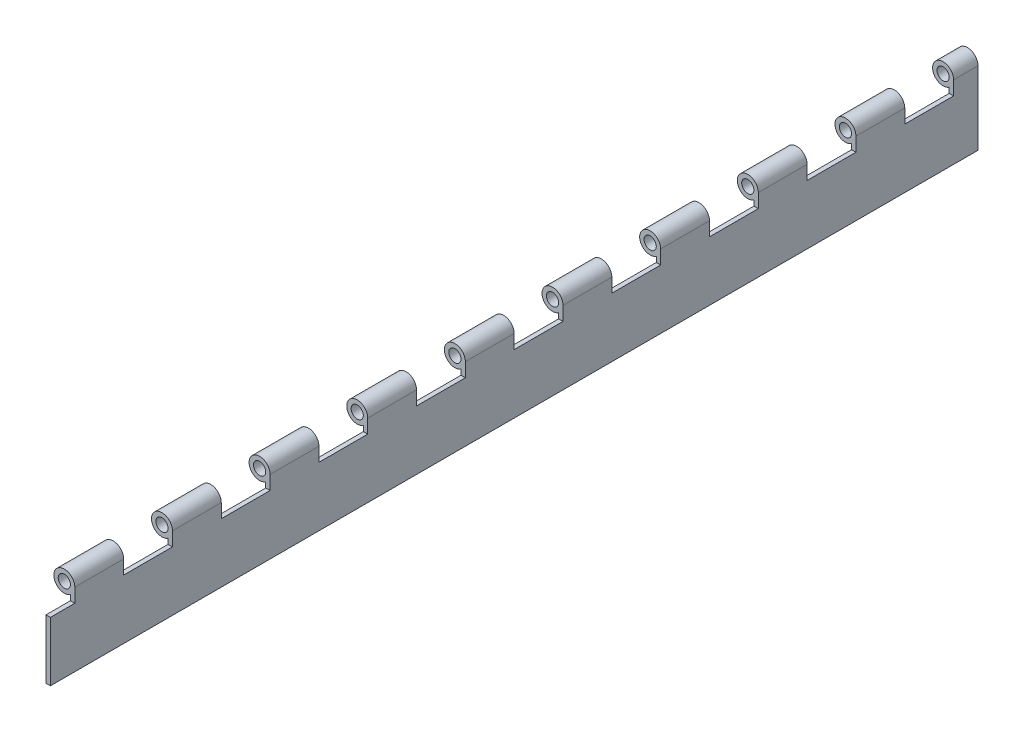
SolidWorks part; units mm, degrees
material "6061 Alloy"
ref_plane "Front Plane" through (0, 0, 0) normal (0, 0, 1) x (1, 0, 0)
ref_plane "Top Plane" through (0, 0, 0) normal (0, 1, 0) x (1, 0, 0)
ref_plane "Right Plane" through (0, 0, 0) normal (1, 0, 0) x (0, 0, -1)
sketch "Sketch1" plane through (0, 0, 0) normal (0, 0, 1) x (1, 0, 0)
  line L0 (5.461, 0) -> (5.461, -38.1)
  line L1 (5.461, -38.1) -> (3.175, -38.1)
  line L2 (3.175, -38.1) -> (3.175, -4.4432)
  circle A0 centre (0, 0) radius 3.175
  arc A1 (5.461, 0) -> (3.175, -4.4432) centre (0, 0) ccw
  circle A2 centre (0, 0) radius 5.461 construction
  dimension "D1" = 6.35
  dimension "D3" = 2.286
  dimension "D4" = 38.1
  dimension "D2" = 2.286
extrude "Boss-Extrude1" add sketch "Sketch1" along normal blind 508
sketch "Sketch2" plane through (5.461, 0, 0) normal (1, 0, 0) x (0, 0, -1)
  line L1 (-508, 5.461) -> (-482.6, 5.461)
  line L2 (-508, 5.461) -> (-508, -7.239)
  line L3 (-508, -7.239) -> (-482.6, -7.239)
  line L4 (-482.6, 5.461) -> (-482.6, -7.239)
  dimension "D1" = 12.7
  dimension "D2" = 25.4
extrude "Cut-Extrude1" cut sketch "Sketch2" against normal through all
pattern_linear "LPattern1" count 10 spacing 50.8 along (0, 0, -1) of "Cut-Extrude1"
sketch "Sketch4" plane through (5.461, 0, 0) normal (1, 0, 0) x (0, 0, -1)
  line L0 (-508, -7.239) -> (-482.6, -7.239) construction
  line L1 (-508, -38.1) -> (-495.3, -38.1)
  line L2 (-508, -38.1) -> (-508, -7.239)
  line L3 (-508, -7.239) -> (-495.3, -7.239)
  line L4 (-495.3, -38.1) -> (-495.3, -7.239)
  line L5 (0, 5.461) -> (-25.4, 5.461) construction
  line L6 (0, -38.1) -> (-12.7, -38.1)
  line L7 (0, -38.1) -> (0, 5.461)
  line L8 (0, 5.461) -> (-12.7, 5.461)
  line L9 (-12.7, -38.1) -> (-12.7, 5.461)
  dimension "D1" = 12.7
extrude "Cut-Extrude2" cut sketch "Sketch4" against normal through all
